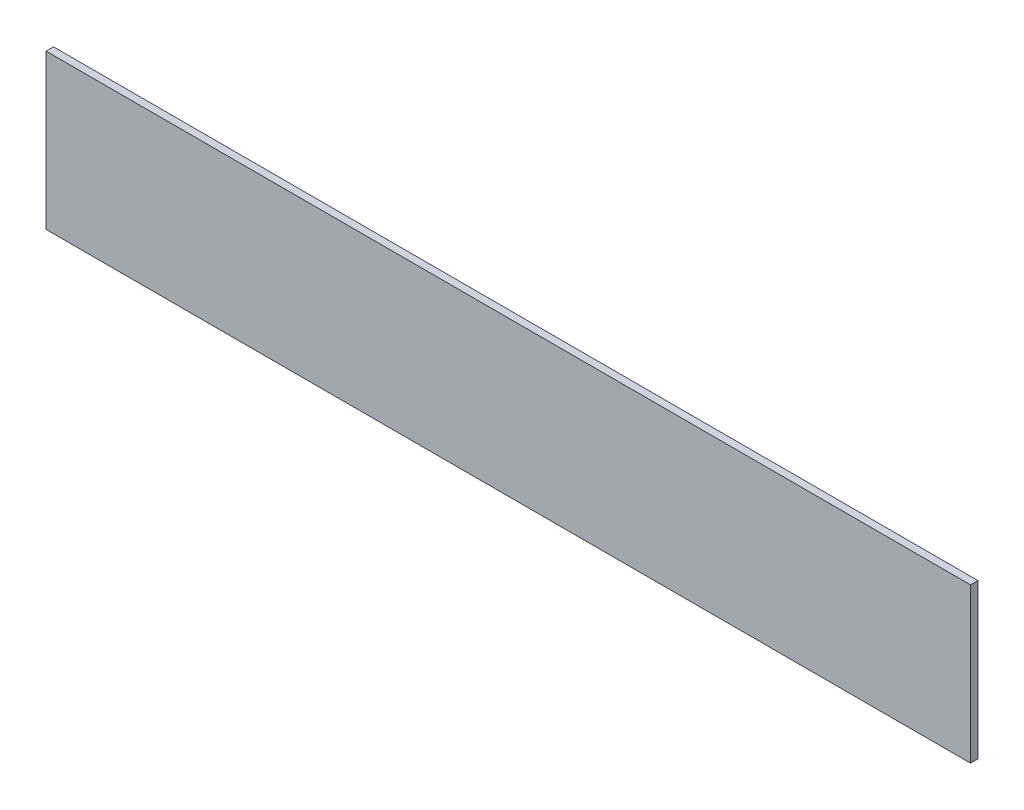
SolidWorks part; units mm, degrees
material "6061 Alloy"
ref_plane "Front Plane" through (0, 0, 0) normal (0, 0, 1) x (1, 0, 0)
ref_plane "Top Plane" through (0, 0, 0) normal (0, 1, 0) x (1, 0, 0)
ref_plane "Right Plane" through (0, 0, 0) normal (1, 0, 0) x (0, 0, -1)
sketch "Sketch1" plane through (0, 0, 0) normal (0, 0, 1) x (1, 0, 0)
  line L0 (190.0936, 63.5) -> (190.0936, 0) construction
  line L1 (0, 0) -> (380.1872, 0)
  line L2 (0, 0) -> (0, 63.5)
  line L3 (0, 63.5) -> (380.1872, 63.5)
  line L4 (380.1872, 0) -> (380.1872, 63.5)
  line L5 (151.9936, 63.5) -> (151.9936, 0) construction
  line L6 (228.1936, 63.5) -> (228.1936, 0) construction
  line L7 (151.9936, 7.9248) -> (228.1936, 7.9248) construction
  line L8 (228.1936, 50.8) -> (151.9936, 50.8) construction
  line L9 (158.3436, 50.8) -> (158.3436, 7.9248) construction
  circle A0 centre (158.3436, 44.45) radius 2.54 construction
  circle A1 centre (158.3436, 14.2748) radius 2.54 construction
  circle A2 centre (221.8436, 14.2748) radius 2.54 construction
  circle A3 centre (221.8436, 44.45) radius 2.54 construction
  dimension "D8" = 6.35
  dimension "D10" = 5.08
  dimension "D1" = 63.5
  dimension "D2" = 380.1872
  dimension "D3" = 38.1
  dimension "D4" = 38.1
  dimension "D5" = 7.9248
  dimension "D6" = 42.8752
  dimension "D7" = 6.35
  dimension "D9" = 6.35
extrude "Boss-Extrude1" add sketch "Sketch1" along normal blind 3.048
equation "\"base length\" = 21"
equation "\"glass pane length\" = 14.125"
equation "\"glass pane width\" = 10.1875"
equation "\"glass pane wall width\" = 3/4"
equation "\"glass lip\" = 1/4"
equation "\"bolt diameter\" = 0.2"
equation "\"stepper body width\" = 2.22"
equation "\"stepper mount offset\" = 0.19"
equation "\"stepper mount diameter\" = 0.19"
equation "\"stepper shaft offset from body\" = 0.79"
equation "\"stepper spacer thickness\" = 0.2"
equation "\"y axis stepper wall height off base\" = 8"
equation "\"y axis stepper wall bracket thickness\" = 1"
equation "\"y axis stepper wall mount side offset\" = 1/2"
equation "\"y axis stepper wall mount top offset\" = 1/2"
equation "\"y axis stepper wall width\" = \"stepper body width\" + 1                  "
equation "\"thin metal\" = 0.12"
equation "\"thick metal\" = 0.25"
equation "\"foot diameter\"= 0.2"
equation "\"foot inset from corner\"= 1"
equation "\"recognizer width\" = 2.5"
equation "\"D1@Sketch1\"=\"recognizer width\""
equation "\"D1@Boss-Extrude1\" = \"thin metal\""
equation "\"y axis bracket height to hole\"= 3.5"
equation "\"recognizer nut plate height\" = 1.25"
equation "\"recognizer nut plate offset\" = 1.5"
equation "\"base width\" = 16.5"
equation "\"recognizer arm length\"= 7"
equation "\"recognizer bracket length\" = 4"
equation "\"D2@Sketch1\"=\"base width\"-\"thin metal\"-1.782+2*\"thin metal\" +0.13"
equation "\"recognizer arm height to hole\"= 4.255"
